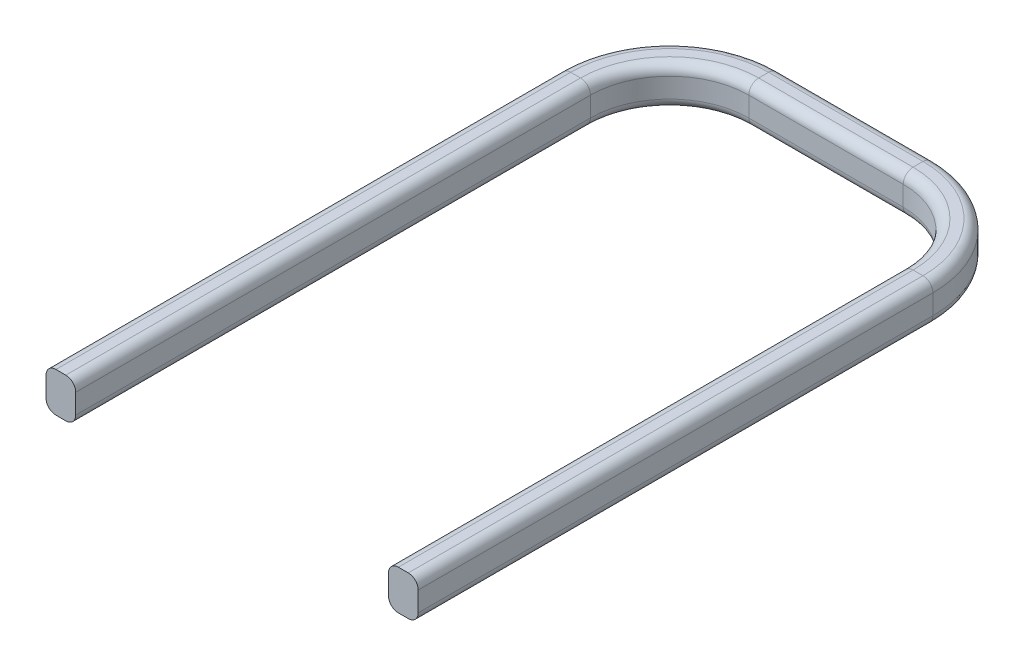
SolidWorks part; units mm, degrees
ref_plane "Ön Düzlem" through (0, 0, 0) normal (0, 0, 1) x (1, 0, 0)
ref_plane "Üst Düzlem" through (0, 0, 0) normal (0, 1, 0) x (1, 0, 0)
ref_plane "Sağ Düzlem" through (0, 0, 0) normal (1, 0, 0) x (0, 0, -1)
sketch "Sketch2" plane through (0, 0, 0) normal (0, 1, 0) x (1, 0, 0)
  line L2 (-3.95, 0) -> (-3.95, 13)
  line L3 (-1.95, 15) -> (1.95, 15)
  line L4 (3.95, 0) -> (3.95, 13)
  arc A0 (1.95, 15) -> (3.95, 13) centre (1.95, 13) cw
  arc A1 (-1.95, 15) -> (-3.95, 13) centre (-1.95, 13) ccw
  point P10 (-3.95, 15)
  dimension "D4" = 2
  dimension "D1" = 15
  dimension "D2" = 3.95
  dimension "D3" = 3.95
sketch "Sketch3" plane through (0, 0, 0) normal (0, 0, 1) x (1, 0, 0)
  line L1 (-3.95, 0) -> (-4.7, 0)
  line L2 (-3.95, 0) -> (-3.95, 1)
  line L3 (-3.95, 1) -> (-4.7, 1)
  line L4 (-4.7, 0) -> (-4.7, 1)
  dimension "D1" = 0.75
  dimension "D2" = 1
sweep "Sweep1" add profiles "Sketch3" path "Sketch2"
fillet "Fillet1" radius 0.25 20 edges at (4.7, 1, -6.5) (3.8945, 1, -14.9445) (0, 1, -15.75) (-3.8945, 1, -14.9445) (4.7, 0, -6.5) (3.8945, 0, -14.9445) (0, 0, -15.75) (-3.8945, 0, -14.9445) (3.95, 0, -6.5) (3.3642, 0, -14.4142) (0, 0, -15) (-3.3642, 0, -14.4142) (3.95, 1, -6.5) (3.3642, 1, -14.4142) (0, 1, -15) (-3.3642, 1, -14.4142) (-4.7, 1, -6.5) (-4.7, 0, -6.5) (-3.95, 0, -6.5) (-3.95, 1, -6.5)
